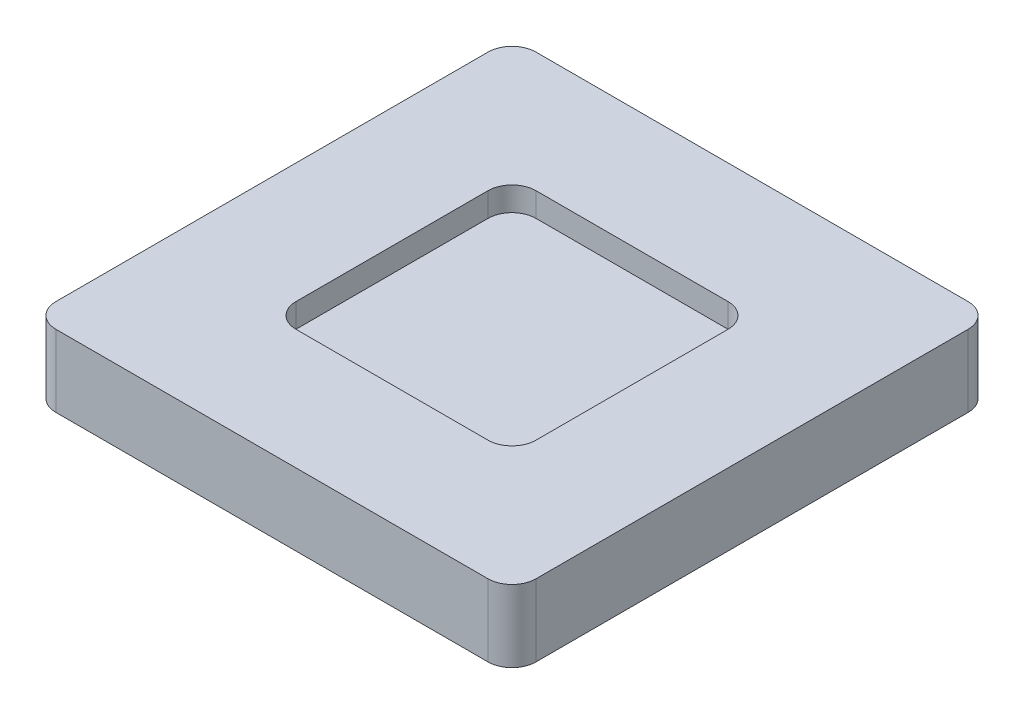
SolidWorks part; units mm, degrees
ref_plane "Front Plane" through (0, 0, 0) normal (0, 0, 1) x (1, 0, 0)
ref_plane "Top Plane" through (0, 0, 0) normal (0, 1, 0) x (1, 0, 0)
ref_plane "Right Plane" through (0, 0, 0) normal (1, 0, 0) x (0, 0, -1)
sketch "Sketch1" plane through (0, 0, 0) normal (0, 1, 0) x (1, 0, 0)
  line L1 (10, 10) -> (-10, 10)
  line L2 (10, 10) -> (10, -10)
  line L3 (10, -10) -> (-10, -10)
  line L4 (-10, 10) -> (-10, -10)
  line L5 (10, 10) -> (-10, -10) construction
  line L6 (10, -10) -> (-10, 10) construction
  point P0 (0, 0)
  dimension "D1" = 20
extrude "Boss-Extrude1" add sketch "Sketch1" along normal blind 3
sketch "Sketch2" plane through (0, 3, 0) normal (0, 1, 0) x (1, 0, 0)
  line L1 (5, 5) -> (-5, 5)
  line L2 (5, 5) -> (5, -5)
  line L3 (5, -5) -> (-5, -5)
  line L4 (-5, 5) -> (-5, -5)
  line L5 (5, 5) -> (-5, -5) construction
  line L6 (5, -5) -> (-5, 5) construction
  point P0 (0, 0)
  dimension "D1" = 10
extrude "Cut-Extrude1" cut sketch "Sketch2" against normal blind 1
fillet "Fillet1" radius 1 8 edges at (5, 2.5, -5) (-5, 2.5, 5) (5, 2.5, 5) (-10, 1.5, -10) (-5, 2.5, -5) (10, 1.5, -10) (10, 1.5, 10) (-10, 1.5, 10)
sketch "Sketch3" plane through (0, 3, 0) normal (0, 1, 0) x (1, 0, 0)
  line L0 (-9, -10) -> (9, -10) construction
  line L1 (-10, 10) -> (10, 10)
  line L2 (-10, 10) -> (-10, -10)
  line L3 (-10, -10) -> (10, -10)
  line L4 (10, 10) -> (10, -10)
  line L5 (-10, 10) -> (10, -10) construction
  line L6 (-10, -10) -> (10, 10) construction
  line L7 (10, -9) -> (10, 9) construction
  point P0 (0, 0)
